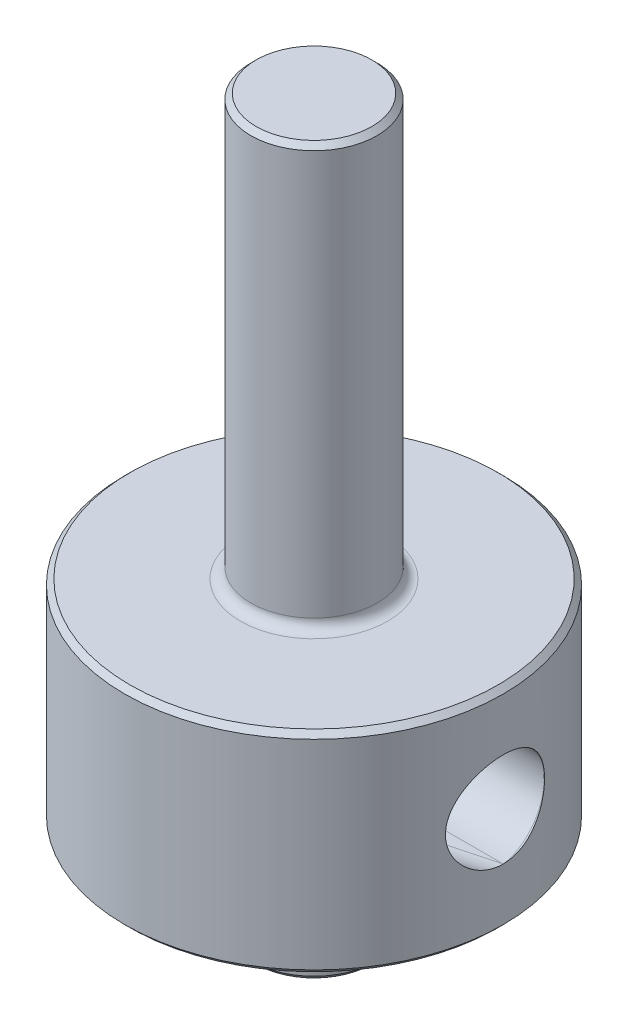
SolidWorks part; units mm, degrees
ref_plane "Plano frontal" through (0, 0, 0) normal (0, 0, 1) x (1, 0, 0)
ref_plane "Plano superior" through (0, 0, 0) normal (0, 1, 0) x (1, 0, 0)
ref_plane "Plano direito" through (0, 0, 0) normal (1, 0, 0) x (0, 0, -1)
sketch "Esboço1" plane through (0, 0, 0) normal (0, 0, 1) x (1, 0, 0)
  line L0 (0, 0) -> (0, 26.74) construction
  line L1 (0, 0) -> (9, 0) construction
  line L2 (0, 25) -> (3, 25)
  line L3 (3, 5) -> (3, 25)
  line L4 (9, 5) -> (3, 5)
  line L11 (9, 5) -> (9, -5)
  line L12 (0, 25) -> (0, 0)
  line L17 (3, -5) -> (9, -5)
  line L18 (3, -9.5) -> (3, -5)
  line L21 (3, -9.5) -> (0, -9.5)
  line L22 (0, -9.5) -> (0, 0)
  point P16 (9, 0)
  dimension "D1" = 6
  dimension "D2" = 6
  dimension "D5" = 18
  dimension "D6" = 20
  dimension "D7" = 10
  dimension "D9" = 4.5
revolve "Revolução1" add sketch "Esboço1" angle 360 about L0
ref_plane "Plano1" through (-9, 0, 0) normal (-1, 0, 0) x (0, 0, 1)
ref_plane "Plano2" through (9, 0, 0) normal (1, 0, 0) x (0, 0, -1)
sketch "Esboço2" plane through (-9, 0, 0) normal (-1, 0, 0) x (0, 0, 1)
  circle A0 centre (0, 0) radius 2.25
  dimension "D1" = 4.5
extrude "Corte-extrusão2" cut sketch "Esboço2" against normal through all
sketch "Esboço4" plane through (0, 0, 0) normal (0, 1, 0) x (1, 0, 0)
  line L0 (9, 0) -> (-9, 0)
  line L1 (0, 0) -> (-7.7942, -4.5) construction
  line L2 (9, 0) -> (-7.7942, -4.5)
  arc A0 (8.7142, -2.25) -> (8.7142, 2.25) centre (0, 0) ccw construction
  circle A1 centre (0, 0) radius 9 construction
  dimension "D1" = 30
ref_plane "Plano3" through (-7.7942, 0, 4.5) normal (-0.9659, 0, 0.2588) x (0.2588, 0, 0.9659)
sketch "Esboço7" plane through (-7.7942, 0, 4.5) normal (-0.9659, 0, 0.2588) x (0.2588, 0, 0.9659)
  circle A0 centre (0, 0) radius 2.25
  dimension "D1" = 4.5
extrude "Corte-extrusão6" cut sketch "Esboço7" against normal through all both and the other way through all
sketch "Sketch1" plane through (0, 0, 0) normal (0, 1, 0) x (1, 0, 0)
  line L0 (9, 0) -> (-10.8444, 0)
  line L1 (-10.8444, 0) -> (-10.4288, -5.2059)
  line L2 (-10.4288, -5.2059) -> (9, 0)
  line L3 (9, 0) -> (-7.7942, -4.5) construction
extrude "Cut-Extrude1" cut sketch "Sketch1" against normal mid plane 4.5
sketch "Sketch2" plane through (0, 0, 0) normal (0, 0, 1) x (1, 0, 0)
  line L0 (8.5, -5) -> (9, 5)
  line L1 (-9, -5) -> (9, -5) construction
  line L2 (9, -55) -> (9, 55) construction
  line L3 (9, 5) -> (-9, 5) construction
  line L4 (9, 5) -> (9, -5)
  line L5 (9, -5) -> (8.5, -5)
  dimension "D1" = 0.5
revolve "Cut-Revolve1" [suppressed] cut sketch "Sketch2" angle 360
fillet "Fillet1" radius 0.5 2 edges at (0, -5, -3) (0, 5, -3)
chamfer "Chamfer1" distance 0.25 angle 45 2 edges at (0, -9.5, -3) (0, 25, -3)
chamfer "Chamfer3" [suppressed] distance 0.25 angle 45
chamfer "Chamfer4" distance 0.25 angle 45 2 edges at (0, -5, -9) (0, 5, -9)
